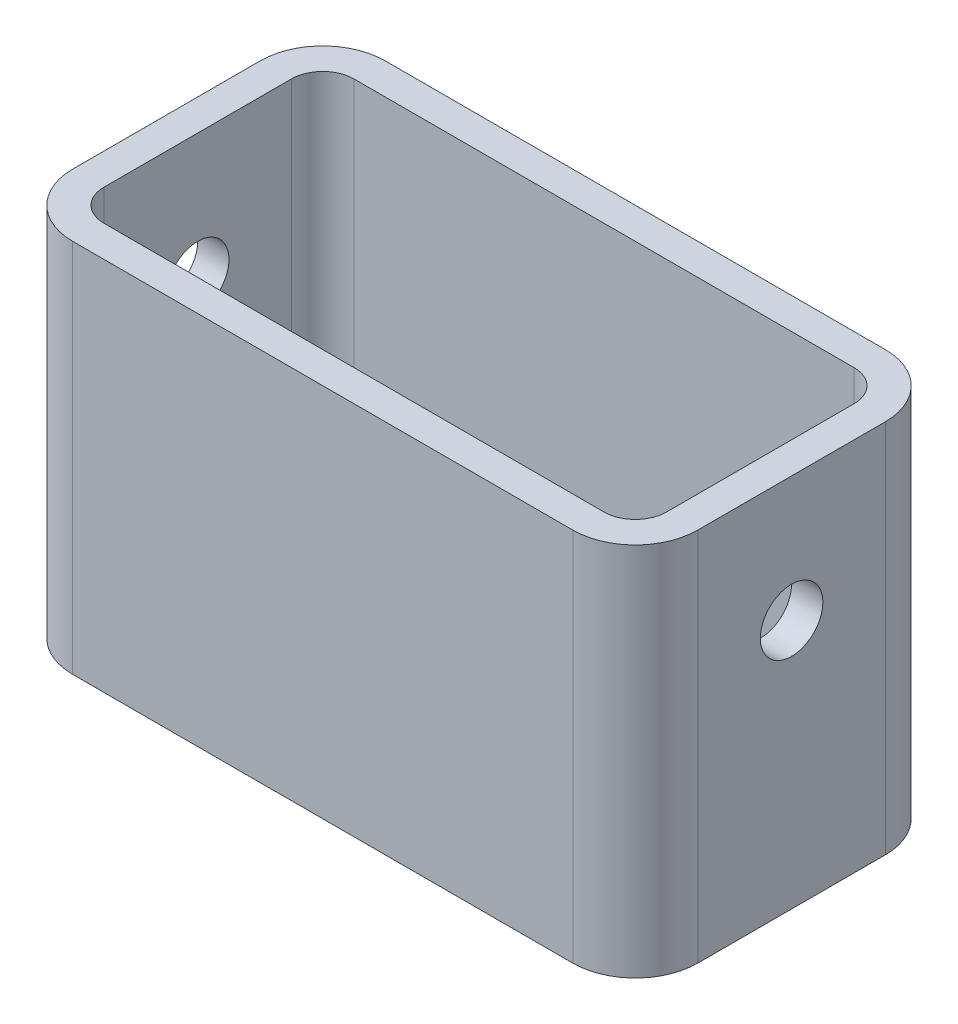
SolidWorks part; units mm, degrees
ref_plane "Front Plane" through (0, 0, 0) normal (0, 0, 1) x (1, 0, 0)
ref_plane "Top Plane" through (0, 0, 0) normal (0, 1, 0) x (1, 0, 0)
ref_plane "Right Plane" through (0, 0, 0) normal (1, 0, 0) x (0, 0, -1)
sketch "Sketch1" plane through (0, 0, 0) normal (0, 1, 0) x (1, 0, 0)
  line L1 (0, 0) -> (100, 0)
  line L2 (0, 0) -> (0, 50)
  line L3 (0, 50) -> (100, 50)
  line L4 (100, 0) -> (100, 50)
  dimension "D1" = 100
  dimension "D2" = 50
extrude "Boss-Extrude1" add sketch "Sketch1" along normal blind 60
fillet "Fillet2" radius 10 4 edges at (0, 30, 0) (0, 30, -50) (100, 30, 0) (100, 30, -50)
sketch3d "3DSketch1"
  line L0 (10, 60, -5) -> (90, 60, -5)
  line L1 (95, 60, -10) -> (95, 60, -40)
  line L2 (90, 60, -45) -> (10, 60, -45)
  line L3 (5, 60, -40) -> (5, 60, -10)
  line L4 (10, 60, -5) -> (90, 60, -5)
  line L5 (95, 60, -10) -> (95, 60, -40)
  line L6 (90, 60, -45) -> (10, 60, -45)
  line L7 (5, 60, -40) -> (5, 60, -10)
  arc A0 (90, 60, -5) -> (95, 60, -10) centre (90, 60, -10) ccw
  arc A1 (95, 60, -40) -> (90, 60, -45) centre (90, 60, -40) ccw
  arc A2 (10, 60, -45) -> (5, 60, -40) centre (10, 60, -40) ccw
  arc A3 (5, 60, -10) -> (10, 60, -5) centre (10, 60, -10) ccw
  arc A4 (90, 60, -5) -> (95, 60, -10) centre (90, 60, -10) ccw
  arc A5 (95, 60, -40) -> (90, 60, -45) centre (90, 60, -40) ccw
  arc A6 (10, 60, -45) -> (5, 60, -40) centre (10, 60, -40) ccw
  arc A7 (5, 60, -10) -> (10, 60, -5) centre (10, 60, -10) ccw
  point P4 (90, 65, -10)
  point P8 (90, 65, -40)
  point P12 (10, 65, -40)
  point P15 (10, 65, -10)
  point P16 (90, 65, -10)
  point P17 (90, 65, -40)
  point P18 (10, 65, -40)
  point P19 (10, 65, -10)
  dimension "D1" = 5
extrude "Cut-Extrude1" cut sketch "3DSketch1" along direction (0, -1, 0) on the side against the normal blind 80 contours L4 A4 L5 A5 L6 A6 L7 A7
sketch "Sketch2" plane through (0, 0, 0) normal (-1, 0, 0) x (0, 0, 1)
  line L0 (-40, 0) -> (-10, 0) construction
  line L1 (-50, 0) -> (-50, 60) construction
  circle A0 centre (-25, 40) radius 5
  dimension "D3" = 10
  dimension "D1" = 40
  dimension "D2" = 25
extrude "Cut-Extrude2" cut sketch "Sketch2" against normal through all
